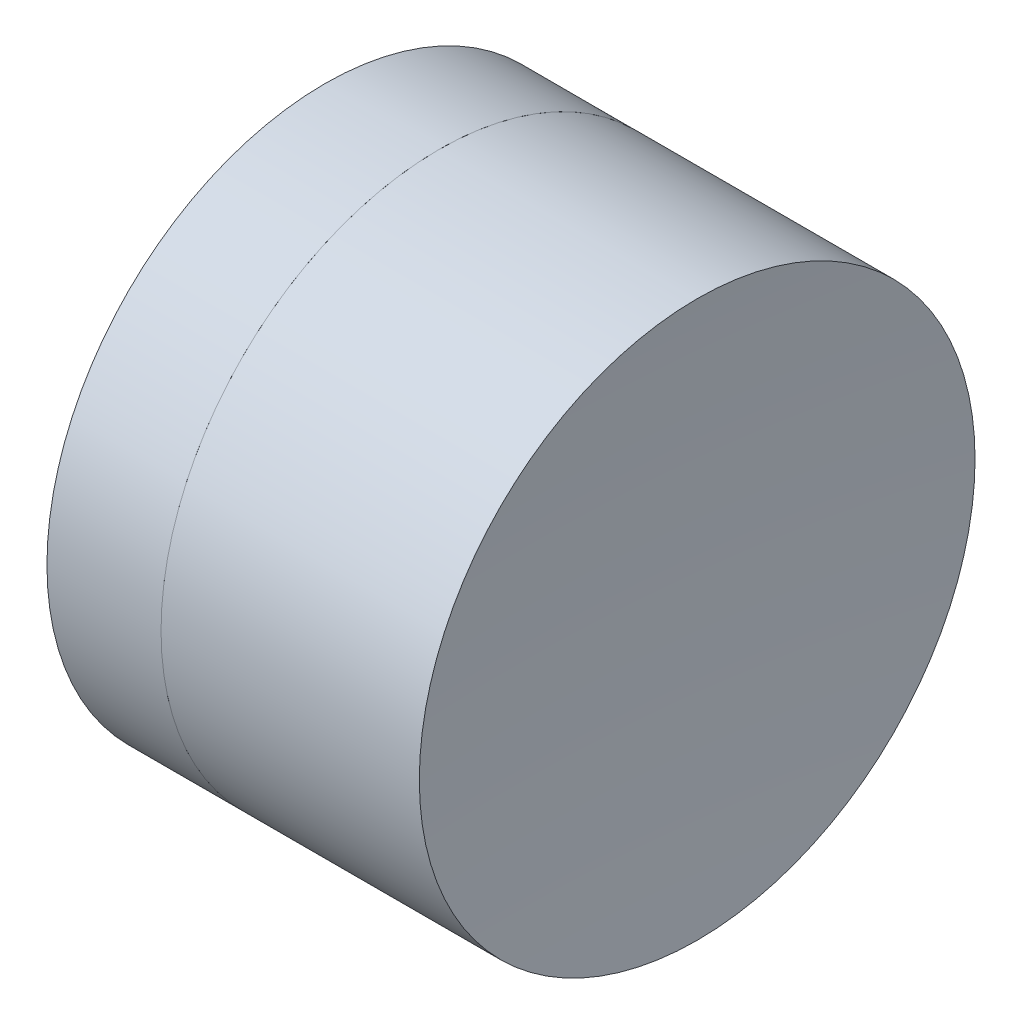
SolidWorks part; units mm, degrees
ref_plane "前视基准面" through (0, 0, 0) normal (0, 0, 1) x (1, 0, 0)
ref_plane "上视基准面" through (0, 0, 0) normal (0, 1, 0) x (1, 0, 0)
ref_plane "右视基准面" through (0, 0, 0) normal (1, 0, 0) x (0, 0, -1)
sketch "草图1" plane through (0, 0, 0) normal (0, 1, 0) x (1, 0, 0)
  line L0 (-0.8161, 0) -> (3.5052, 0) construction
  line L1 (1.3328, -2.5) -> (2.3593, -2.5)
  line L2 (1.3328, 2.5) -> (2.3593, 2.5)
  arc A0 (2.3593, -2.5) -> (2.3593, 2.5) centre (-1.514, 0) ccw
  arc A1 (1.3328, 2.5) -> (1.3328, -2.5) centre (5.206, 0) ccw
  point P10 (0.596, 0)
  point P11 (3.096, 0)
  dimension "D3" = 4.61
  dimension "D4" = 4.61
  dimension "D1" = 2.5
  dimension "D2" = 2.5
  dimension "D5" = 2.5
revolve "旋转1" add sketch "草图1" angle 360 about L0
sketch "草图2" plane through (0, 0, 0) normal (0, 1, 0) x (1, 0, 0)
  line L0 (-0.5519, 0) -> (10.2522, 0) construction
  line L2 (2.3593, 2.5) -> (4.6831, 2.5)
  line L3 (2.3593, -2.5) -> (4.6831, -2.5)
  arc A0 (4.6831, 2.5) -> (4.6831, -2.5) centre (40.546, 0) ccw
  arc A1 (2.3593, -2.5) -> (2.3593, 2.5) centre (-1.514, 0) ccw construction
  arc A2 (2.3593, -2.5) -> (2.3593, 2.5) centre (-1.514, 0) ccw
  point P3 (22.8714, 0)
  point P4 (3.096, 0)
  point P10 (4.596, 0)
  dimension "D1" = 35.95
  dimension "D2" = 1.5
revolve "旋转2" add sketch "草图2" angle 360 about L0
